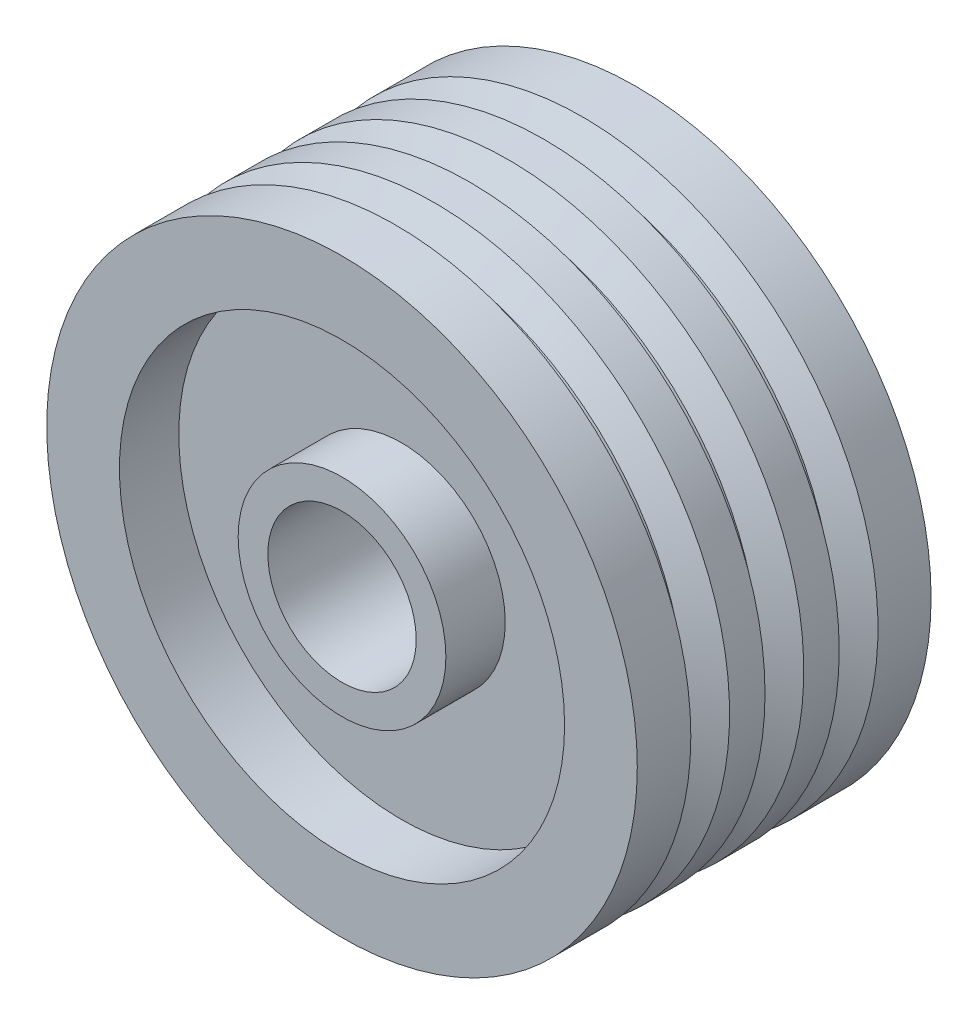
SolidWorks part; units mm, degrees
ref_plane "Front Plane" through (0, 0, 0) normal (0, 0, 1) x (1, 0, 0)
ref_plane "Top Plane" through (0, 0, 0) normal (0, 1, 0) x (1, 0, 0)
ref_plane "Right Plane" through (0, 0, 0) normal (1, 0, 0) x (0, 0, -1)
sketch "Sketch1" plane through (0, 0, 0) normal (0, 0, 1) x (1, 0, 0)
  circle A0 centre (0, 0) radius 99.5
  dimension "D1" = 199
extrude "Boss-Extrude1" add sketch "Sketch1" along normal mid plane 99
sketch "Sketch2" plane through (0, 0, 0) normal (0, 1, 0) x (1, 0, 0)
  line L24 (-99.5, -49.5) -> (99.5, -49.5) construction
  line L25 (0, 0) -> (0, -49.5) construction
  line L28 (-89.9819, -25.9829) -> (-99.9117, -31.695)
  line L34 (-99.9156, -18.1587) -> (-90.0181, -23.8938)
  line L36 (-89.9819, -0.9829) -> (-99.9117, -6.695)
  line L38 (-99.9298, 6.8495) -> (-90.0181, 1.1062)
  line L40 (-90.0166, 23.9972) -> (-99.9117, 18.305)
  line L42 (-99.9298, 31.8495) -> (-90.0181, 26.1062)
  line L46 (-90.0181, 26.1062) -> (-90.0166, 23.9972)
  line L50 (-99.9156, -18.1587) -> (-99.9117, -31.695)
  line L52 (-90.0181, -23.8938) -> (-89.9819, -25.9829)
  line L53 (-99.9298, 6.8495) -> (-99.9117, -6.695)
  line L58 (-99.9298, 31.8495) -> (-99.9117, 18.305)
  line L59 (-90.0181, 1.1062) -> (-89.9819, -0.9829)
  line L61 (-89.9819, 49.0171) -> (-90, 49.0068) [skipped]
  dimension "D2" = 4
revolve "Cut-Revolve1" cut sketch "Sketch2" angle 360 about L25
sketch "Sketch3" plane through (0, 0, -49.5) normal (0, 0, -1) x (-1, 0, 0)
  circle A0 centre (0, 0) radius 75
  circle A1 centre (0, 0) radius 35
  dimension "D1" = 150
  dimension "D2" = 70
extrude "Cut-Extrude1" cut sketch "Sketch3" against normal blind 20
sketch "Sketch4" plane through (0, 0, 49.5) normal (0, 0, 1) x (1, 0, 0)
  circle A1 centre (0, 0) radius 25
  dimension "D1" = 50
extrude "Cut-Extrude2" cut sketch "Sketch4" against normal through all both and the other way through all
sketch "Sketch5" plane through (0, 0, 49.5) normal (0, 0, 1) x (1, 0, 0)
  circle A0 centre (0, 0) radius 35
  circle A1 centre (0, 0) radius 75
  dimension "D1" = 150
  dimension "D2" = 70
extrude "Cut-Extrude3" cut sketch "Sketch5" against normal blind 20
sketch "Sketch7" plane through (0, 0, 0) normal (0, 1, 0) x (1, 0, 0)
  line L0 (99.5, 18.5419) -> (-99.5, 18.5419) construction
  line L1 (-102.9698, 31.3248) -> (-92.1754, 31.3248)
  line L2 (-102.9698, 31.3248) -> (-102.9698, 18.5419)
  line L3 (-102.9698, 18.5419) -> (-92.1754, 18.5419)
  line L4 (-92.1754, 31.3248) -> (-92.1754, 18.5419)
  line L5 (99.5, -6.4581) -> (-99.5, -6.4581) construction
  line L6 (-102.9698, 5.9263) -> (-92.1754, 5.9263)
  line L7 (-102.9698, 5.9263) -> (-102.9698, -6.4581)
  line L8 (-102.9698, -6.4581) -> (-92.1754, -6.4581)
  line L9 (-92.1754, 5.9263) -> (-92.1754, -6.4581)
  line L10 (0, 49.5) -> (0, -49.5) construction
  line L11 (-102.9698, -18.4139) -> (-92.1754, -18.4139)
  line L12 (-102.9698, -18.4139) -> (-102.9698, -31.1132)
  line L13 (-102.9698, -31.1132) -> (-92.1754, -31.1132)
  line L14 (-92.1754, -18.4139) -> (-92.1754, -31.1132)
  line L15 (25, 49.5) -> (-25, 49.5) construction
  line L16 (-99.5, -49.5) -> (99.5, -49.5) construction
  line L18 (-92.1754, -31.1132) -> (-102.9698, -31.1132)
  line L20 (-92.1754, -18.4139) -> (-102.9698, -18.4139)
  line L21 (92.1754, -18.4139) -> (102.9698, -18.4139)
  line L22 (92.1754, -31.1132) -> (102.9698, -31.1132)
  line L23 (92.1754, -18.4139) -> (92.1754, -31.1132)
  line L24 (102.9698, -31.1132) -> (92.1754, -31.1132)
  line L25 (102.9698, -18.4139) -> (102.9698, -31.1132)
  line L26 (102.9698, -18.4139) -> (92.1754, -18.4139)
  line L27 (92.1754, 5.9263) -> (92.1754, -6.4581)
  line L28 (102.9698, -6.4581) -> (92.1754, -6.4581)
  line L29 (102.9698, 5.9263) -> (102.9698, -6.4581)
  line L30 (102.9698, 5.9263) -> (92.1754, 5.9263)
  line L31 (92.1754, 31.3248) -> (92.1754, 18.5419)
  line L32 (102.9698, 18.5419) -> (92.1754, 18.5419)
  line L33 (102.9698, 31.3248) -> (102.9698, 18.5419)
  line L34 (102.9698, 31.3248) -> (92.1754, 31.3248)
sketch "Sketch9" plane through (0, 0, 0) normal (1, 0, 0) x (0, 0, -1)
  line L0 (-18.3995, 99.5) -> (-18.3995, -99.5) construction
  line L1 (-31.5817, 103.4236) -> (-18.3995, 103.4236)
  line L2 (-31.5817, 103.4236) -> (-31.5817, 90.4701)
  line L3 (-31.5817, 90.4701) -> (-18.3995, 90.4701)
  line L4 (-18.3995, 103.4236) -> (-18.3995, 90.4701)
  line L5 (6.6005, 99.5) -> (6.6005, -99.5) construction
  line L6 (-6.6302, 103.4236) -> (6.6005, 103.4236)
  line L7 (-6.6302, 103.4236) -> (-6.6302, 90.4701)
  line L8 (-6.6302, 90.4701) -> (6.6005, 90.4701)
  line L9 (6.6005, 103.4236) -> (6.6005, 90.4701)
  line L10 (31.6005, 99.5) -> (31.6005, -99.5) construction
  line L11 (18.6399, 103.4236) -> (31.6005, 103.4236)
  line L12 (18.6399, 103.4236) -> (18.6399, 90.4701)
  line L13 (18.6399, 90.4701) -> (31.6005, 90.4701)
  line L14 (31.6005, 103.4236) -> (31.6005, 90.4701)
  line L15 (-49.5, 0) -> (49.5, 0) construction
  line L16 (-49.5, 99.5) -> (-49.5, -99.5) construction
  line L17 (49.5, 0) -> (-49.5, 0) construction
  line L18 (31.6005, -103.4236) -> (31.6005, -90.4701)
  line L19 (18.6399, -90.4701) -> (31.6005, -90.4701)
  line L20 (18.6399, -103.4236) -> (18.6399, -90.4701)
  line L21 (18.6399, -103.4236) -> (31.6005, -103.4236)
  line L22 (6.6005, -103.4236) -> (6.6005, -90.4701)
  line L23 (-6.6302, -90.4701) -> (6.6005, -90.4701)
  line L24 (-6.6302, -103.4236) -> (-6.6302, -90.4701)
  line L25 (-6.6302, -103.4236) -> (6.6005, -103.4236)
  line L26 (-18.3995, -103.4236) -> (-18.3995, -90.4701)
  line L27 (-31.5817, -90.4701) -> (-18.3995, -90.4701)
  line L28 (-31.5817, -103.4236) -> (-31.5817, -90.4701)
  line L29 (-31.5817, -103.4236) -> (-18.3995, -103.4236)
